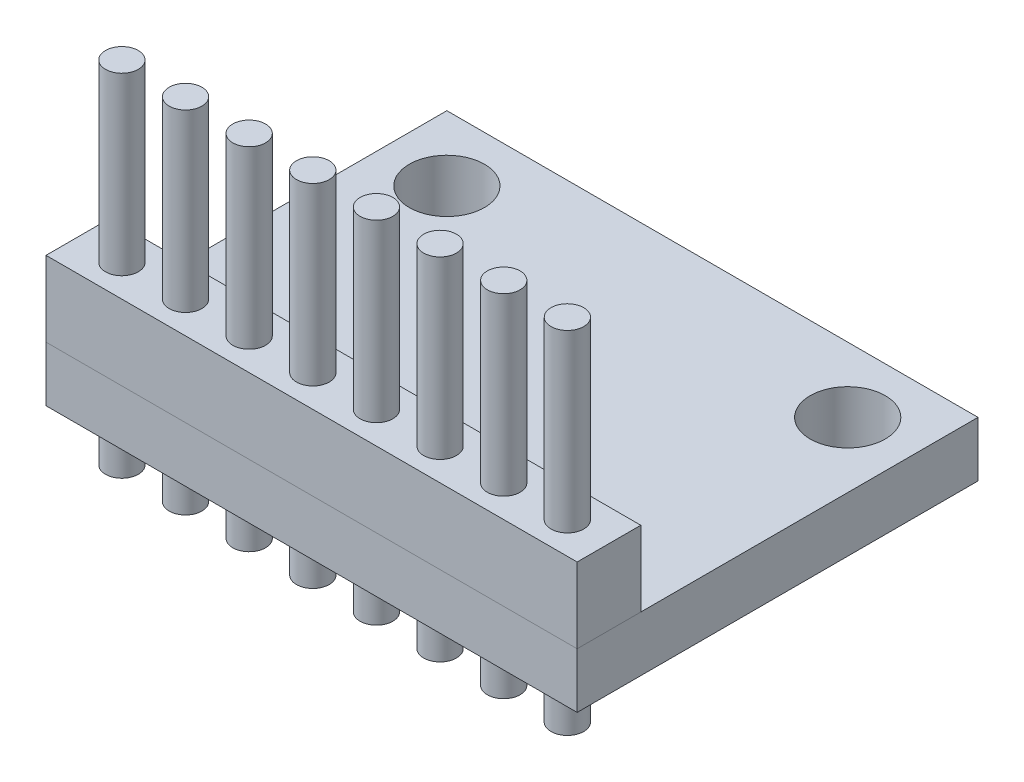
SolidWorks part; units mm, degrees
ref_plane "Front Plane" through (0, 0, 0) normal (0, 0, 1) x (1, 0, 0)
ref_plane "Top Plane" through (0, 0, 0) normal (0, 1, 0) x (1, 0, 0)
ref_plane "Right Plane" through (0, 0, 0) normal (1, 0, 0) x (0, 0, -1)
sketch "Sketch1" plane through (0, 0, 0) normal (0, 1, 0) x (1, 0, 0)
  line L1 (-8.6671, 6.5471) -> (12.5329, 6.5471)
  line L2 (-8.6671, 6.5471) -> (-8.6671, -9.4529)
  line L3 (-8.6671, -9.4529) -> (12.5329, -9.4529)
  line L4 (12.5329, 6.5471) -> (12.5329, -9.4529)
  dimension "D1" = 21.2
  dimension "D2" = 16
extrude "Boss-Extrude1" add sketch "Sketch1" along normal blind 2.2
sketch "Sketch2" plane through (0, 2.2, 0) normal (0, 1, 0) x (1, 0, 0)
  line L0 (12.5329, 6.5471) -> (-8.6671, 6.5471) construction
  line L1 (-8.6671, 6.5471) -> (-8.6671, -9.4529) construction
  line L2 (12.5329, -9.4529) -> (12.5329, 6.5471) construction
  circle A0 centre (-6.0671, 3.9471) radius 1.5
  circle A1 centre (9.9329, 3.9471) radius 1.5
  dimension "D1" = 3
  dimension "D2" = 2.6
  dimension "D3" = 2.6
  dimension "D4" = 2.6
extrude "Cut-Extrude1" cut sketch "Sketch2" against normal blind 2.2
sketch "Sketch3" plane through (0, 2.2, 0) normal (0, 1, 0) x (1, 0, 0)
  line L0 (-8.6671, 6.5471) -> (-8.6671, -9.4529) construction
  line L1 (-8.6671, -9.4529) -> (12.5329, -9.4529) construction
  circle A0 centre (-6.9071, -8.1829) radius 0.6535
  circle A1 centre (-4.3671, -8.1829) radius 0.6535
  circle A2 centre (-1.8271, -8.1829) radius 0.6535
  circle A3 centre (0.7129, -8.1829) radius 0.6535
  circle A4 centre (3.2529, -8.1829) radius 0.6535
  circle A5 centre (5.7929, -8.1829) radius 0.6535
  circle A6 centre (8.3329, -8.1829) radius 0.6535
  circle A7 centre (10.8729, -8.1829) radius 0.6535
  dimension "D2" = 1.76
  dimension "D3" = 1.27
  dimension "D1" = 8
extrude "Boss-Extrude2" add sketch "Sketch3" against normal blind 4 and the other way blind 10
sketch "Sketch4" plane through (0, 2.2, 0) normal (0, 1, 0) x (1, 0, 0)
  line L0 (12.5329, -9.4529) -> (12.5329, 6.5471) construction
  line L1 (-8.6671, -9.4529) -> (12.5329, -9.4529)
  line L2 (-8.6671, -9.4529) -> (-8.6671, -6.9129)
  line L3 (-8.6671, -6.9129) -> (12.5329, -6.9129)
  line L4 (12.5329, -9.4529) -> (12.5329, -6.9129)
  line L5 (-8.6671, 6.5471) -> (-8.6671, -9.4529) construction
  dimension "D1" = 2.54
extrude "Boss-Extrude3" add sketch "Sketch4" along normal blind 3 separate body
sketch "Sketch5" plane through (0, 0, 0) normal (0, -1, 0) x (1, 0, 0)
  line L1 (3.6749, -0.3517) -> (-1.1788, -0.3517)
  line L2 (3.6749, -0.3517) -> (3.6749, 3.6619)
  line L3 (3.6749, 3.6619) -> (-1.1788, 3.6619)
  line L4 (-1.1788, -0.3517) -> (-1.1788, 3.6619)
extrude "Boss-Extrude4" add sketch "Sketch5" along normal blind 1
